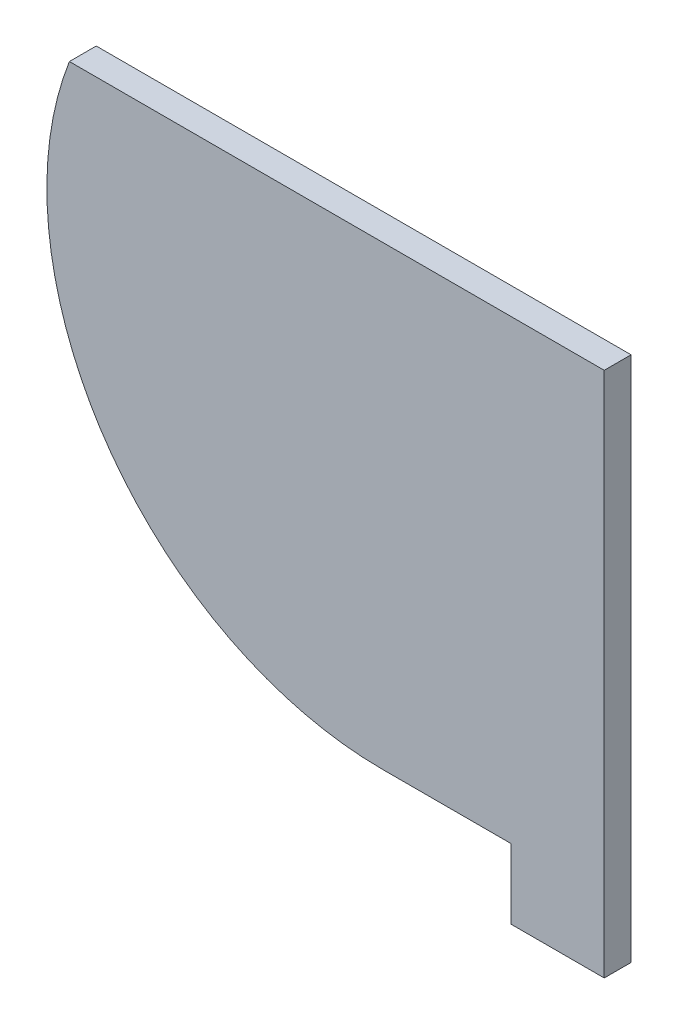
SolidWorks part; units mm, degrees
ref_plane "Front Plane" through (0, 0, 0) normal (0, 0, 1) x (1, 0, 0)
ref_plane "Top Plane" through (0, 0, 0) normal (0, 1, 0) x (1, 0, 0)
ref_plane "Right Plane" through (0, 0, 0) normal (1, 0, 0) x (0, 0, -1)
sketch "Sketch1" plane through (0, 0, 0) normal (0, 0, 1) x (1, 0, 0)
  line L12 (0, 0) -> (0, -85)
  line L13 (-41.2806, -85) -> (0, -85)
  line L14 (0, 0) -> (-99.5901, 0)
  arc A3 (-99.5901, 0) -> (-41.2806, -85) centre (-41.2806, -22.5) ccw
  dimension "D1" = 62.5
  dimension "D2" = 41.2806
  dimension "D3" = 85
extrude "Boss-Extrude1" add sketch "Sketch1" along normal blind 5
sketch "Sketch2" plane through (0, 0, 5) normal (0, 0, 1) x (1, 0, 0)
  line L0 (-17.35, -85) -> (-17.35, -98)
  line L1 (-17.35, -85) -> (0, -85)
  line L2 (-17.35, -98) -> (0, -98)
  line L3 (0, -85) -> (0, -98)
  line L4 (11.3398, -98) -> (-17.8802, -98) construction
  line L8 (-41.2806, -85) -> (0, -85) construction
  line L12 (0.87, -87.011) -> (0.87, -110.6927) construction
  line L13 (0.87, -110) -> (0.87, -107) construction
  line L14 (-18.35, -88.5135) -> (-18.35, -110.6927) construction
  line L15 (-18.35, -107) -> (-18.35, -110) construction
  line L17 (0, -85) -> (0, 0) construction
  dimension "D1" = 1
extrude "Boss-Extrude2" add sketch "Sketch2" against normal blind 5
